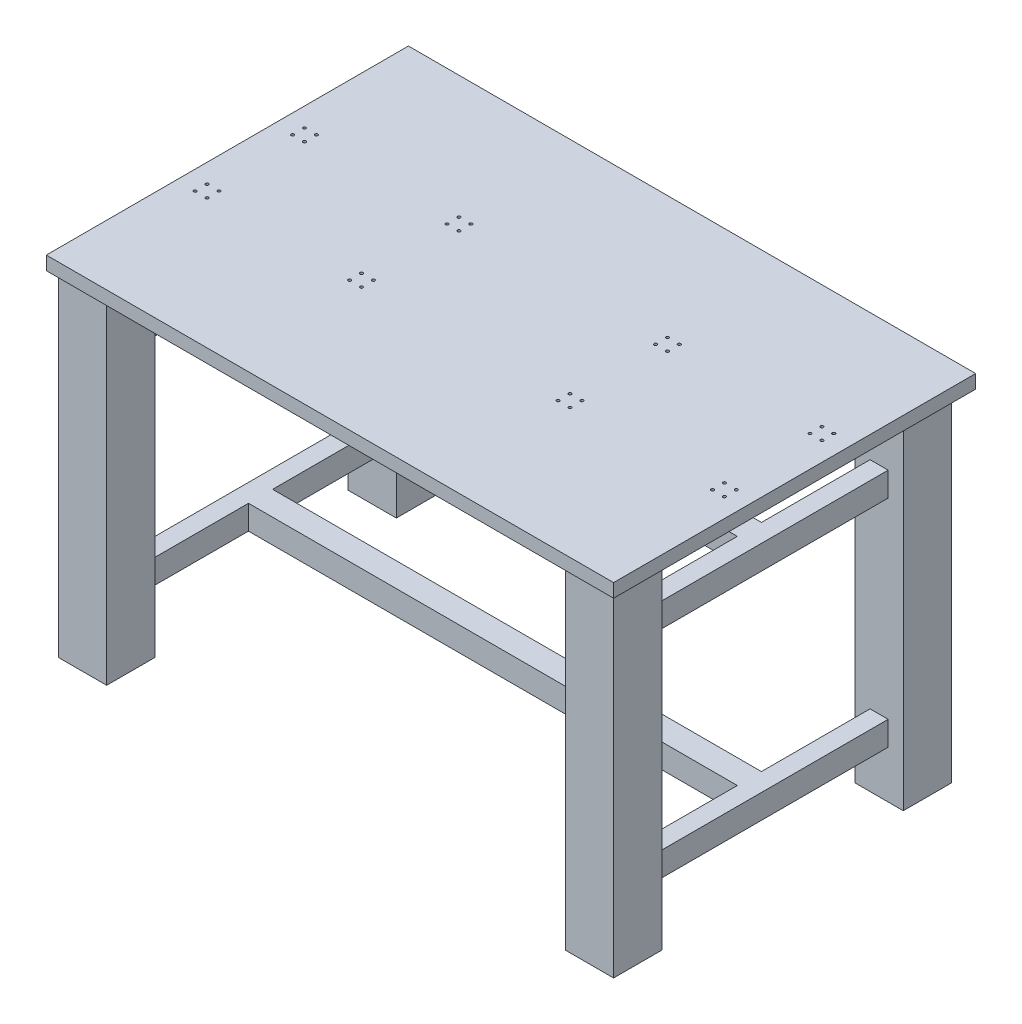
SolidWorks part; units mm, degrees
material "Alloy Steel"
ref_plane "Front Plane" through (0, 0, 0) normal (0, 0, 1) x (1, 0, 0)
ref_plane "Top Plane" through (0, 0, 0) normal (0, 1, 0) x (1, 0, 0)
ref_plane "Right Plane" through (0, 0, 0) normal (1, 0, 0) x (0, 0, -1)
sketch "Sketch1" plane through (0, 0, 0) normal (0, 1, 0) x (1, 0, 0)
  line L0 (-366.1707, 0) -> (17942.3634, 0) construction
  line L1 (0, -366.1707) -> (0, 17942.3634) construction
  line L2 (-584.2, 254) -> (-482.6, 254)
  line L3 (-584.2, -355.6) -> (584.2, -355.6)
  line L4 (-584.2, -355.6) -> (-584.2, 355.6)
  line L5 (-584.2, 355.6) -> (584.2, 355.6)
  line L6 (584.2, -355.6) -> (584.2, 355.6)
  line L7 (0, 355.6) -> (0, -355.6) construction
  line L8 (-584.2, 0) -> (584.2, 0) construction
  line L9 (-482.6, 254) -> (-482.6, 355.6)
  line L10 (482.6, 254) -> (482.6, 355.6)
  line L11 (584.2, 254) -> (482.6, 254)
  line L12 (584.2, -254) -> (482.6, -254)
  line L13 (482.6, -254) -> (482.6, -355.6)
  line L14 (-482.6, -254) -> (-482.6, -355.6)
  line L15 (-584.2, -254) -> (-482.6, -254)
  line L16 (-533.4, 254) -> (-533.4, -254) construction
  line L17 (-552.45, 254) -> (-552.45, -254)
  line L18 (-514.35, 254) -> (-514.35, -254)
  line L19 (514.35, 254) -> (514.35, -254)
  line L20 (552.45, 254) -> (552.45, -254)
  line L21 (-514.35, 25.4) -> (514.35, 25.4)
  line L22 (-514.35, -25.4) -> (514.35, -25.4)
  point P4 (0, 0)
  dimension "D1" = 1168.4
  dimension "D2" = 711.2
  dimension "D3" = 101.6
  dimension "D4" = 38.1
  dimension "D5" = 50.8
extrude "Boss-Extrude1" add sketch "Sketch1" against normal blind 704.85 contours L2 L9 L5 L4 | L11 L6 L5 L10 | L12 L13 L3 L6 | L15 L4 L3 L14 | L18 L2 L17 L15 | L18 L22 L19 L21 | L20 L11 L19 L12
sketch "Sketch2" plane through (0, 0, 0) normal (1, 0, 0) x (0, 0, -1)
  line L0 (254, -704.85) -> (254, 0) construction
  line L1 (-254, 0) -> (254, 0)
  line L2 (-254, 0) -> (-254, -100)
  line L3 (-254, -100) -> (254, -100)
  line L4 (254, 0) -> (254, -100)
  line L5 (-254, -704.85) -> (-254, 0) construction
  line L6 (-254, -150.8) -> (254, -150.8)
  line L7 (-254, -150.8) -> (-254, -554.05)
  line L8 (-254, -554.05) -> (254, -554.05)
  line L9 (254, -150.8) -> (254, -554.05)
  line L10 (254, -704.85) -> (254, 0) construction
  line L11 (-254, -704.85) -> (254, -704.85)
  line L12 (-254, -704.85) -> (-254, -604.85)
  line L13 (-254, -604.85) -> (254, -604.85)
  line L14 (254, -704.85) -> (254, -604.85)
  dimension "D1" = 100
  dimension "D2" = 50.8
  dimension "D3" = 50.8
extrude "Cut-Extrude1" cut sketch "Sketch2" against normal through all both and the other way through all
sketch "Sketch3" plane through (0, 0, 0) normal (0, 1, 0) x (1, 0, 0)
  line L0 (-584.2, -355.6) -> (-482.6, -355.6) construction
  line L1 (-596.9, 393.7) -> (596.9, 393.7)
  line L2 (-596.9, 393.7) -> (-596.9, -368.3)
  line L3 (-596.9, -368.3) -> (596.9, -368.3)
  line L4 (596.9, 393.7) -> (596.9, -368.3)
  line L5 (0, -368.3) -> (0, 393.7) construction
  line L6 (-596.9, 12.7) -> (596.9, 12.7) construction
  point P0 (0, 12.7)
  dimension "D1" = 762
  dimension "D2" = 1193.8
  dimension "D3" = 12.7
extrude "Boss-Extrude2" add sketch "Sketch3" along normal blind 28.5 separate body
sketch "Sketch4" plane through (0, 28.5, 0) normal (0, 1, 0) x (1, 0, 0)
  line L0 (-596.9, 20) -> (596.9, 20) construction
  line L1 (-596.9, 393.7) -> (-596.9, -368.3) construction
  line L2 (596.9, -368.3) -> (596.9, 393.7) construction
  line L3 (-556.9, 110) -> (-531.9, 110) construction
  line L4 (-556.9, 110) -> (-556.9, 135) construction
  line L5 (-556.9, 135) -> (-231.9, 135) construction
  circle A0 centre (-556.9, 110) radius 3.1
  circle A1 centre (-531.9, 110) radius 3.1
  circle A2 centre (-531.9, 135) radius 3.1
  circle A3 centre (-556.9, 135) radius 3.1
  circle A4 centre (-231.9, 135) radius 3.1
  circle A5 centre (-206.9, 135) radius 3.1
  circle A6 centre (-231.9, 110) radius 3.1
  circle A7 centre (-206.9, 110) radius 3.1
  circle A8 centre (-206.9, -70) radius 3.1
  circle A9 centre (-231.9, -70) radius 3.1
  circle A10 centre (-231.9, -95) radius 3.1
  circle A11 centre (-206.9, -95) radius 3.1
  circle A12 centre (-531.9, -70) radius 3.1
  circle A13 centre (-531.9, -95) radius 3.1
  circle A14 centre (-556.9, -70) radius 3.1
  circle A15 centre (-556.9, -95) radius 3.1
  dimension "D2" = 180
  dimension "D3" = 40
  dimension "D4" = 6.2
  dimension "D1" = 20
  dimension "D7" = 25
  dimension "D8" = 25
  dimension "D10" = 325
  dimension "D5" = 2
  dimension "D6" = 2
  dimension "D9" = 2
extrude "Cut-Extrude2" cut sketch "Sketch4" against normal up to surface (28.5 mm away) up to face at (0, 0, -12.7)
mirror "Mirror1" about plane through (0, 0, 0) normal (1, 0, 0) of "Cut-Extrude2"
